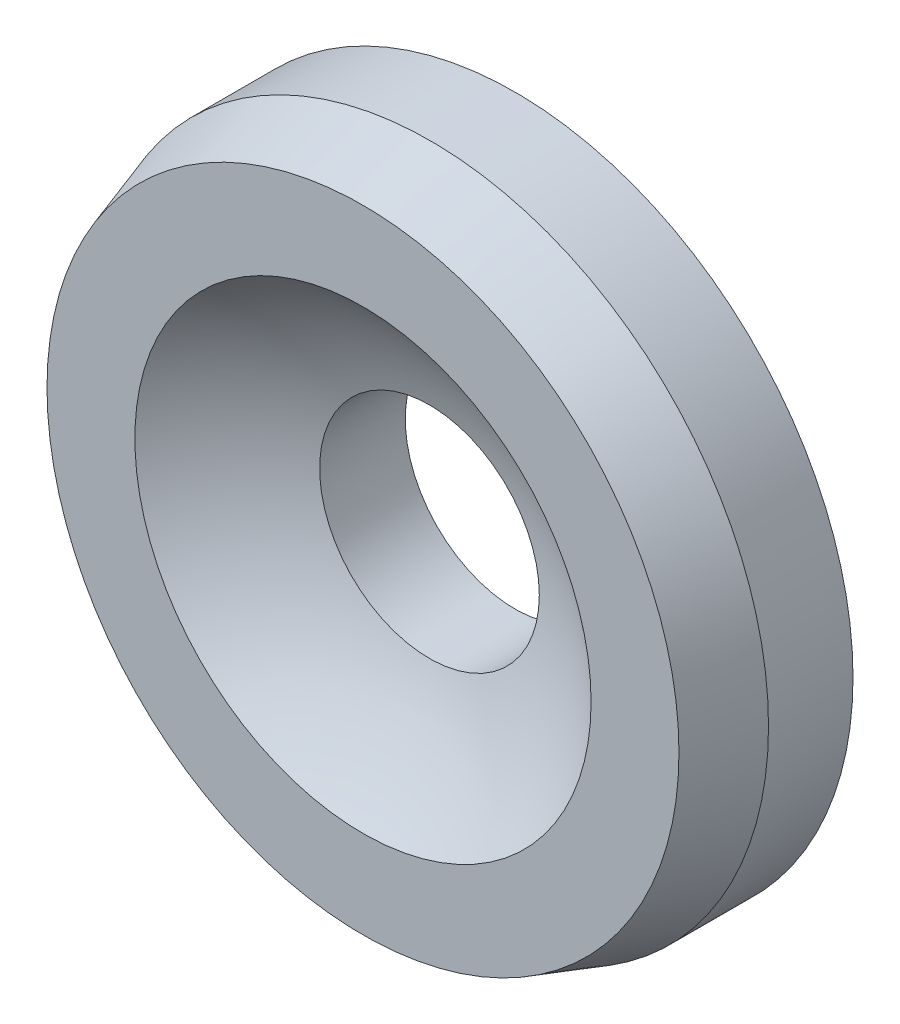
SolidWorks part; units mm, degrees
ref_plane "Alzado" through (0, 0, 0) normal (0, 0, 1) x (1, 0, 0)
ref_plane "Planta" through (0, 0, 0) normal (0, 1, 0) x (1, 0, 0)
ref_plane "Vista lateral" through (0, 0, 0) normal (1, 0, 0) x (0, 0, -1)
ref_plane "Plane1" through (0, -6.0741, 0) normal (0, 1, 0) x (1, 0, 0)
sketch "Sketch1" plane through (0, -6.0741, 0) normal (0, 1, 0) x (1, 0, 0)
  line L0 (-1.6623, -1.57) -> (-1.6623, -1.32)
  line L1 (-1.6623, -1.32) -> (-2.3373, -1.32)
  line L2 (-2.3373, -1.32) -> (-2.3373, -1.5733)
  line L3 (-1.9873, -1.77) -> (-1.7272, -1.77)
  line L4 (-1.7272, -1.77) -> (-1.6623, -1.57)
  line L5 (-2.6623, -1.32) -> (-2.6623, -1.77) construction
  arc A0 (-2.3373, -1.5733) -> (-1.9873, -1.77) centre (-2.6623, -2.5612) cw
  dimension "D1" = 1.04
  dimension "D2" = 0.325
  dimension "D3" = 0.675
  dimension "D4" = 0.935
  dimension "D5" = 1
  dimension "D6" = 0.25
  dimension "D7" = 0.2533
revolve "Revolve1" add sketch "Sketch1" angle 360 about L5
